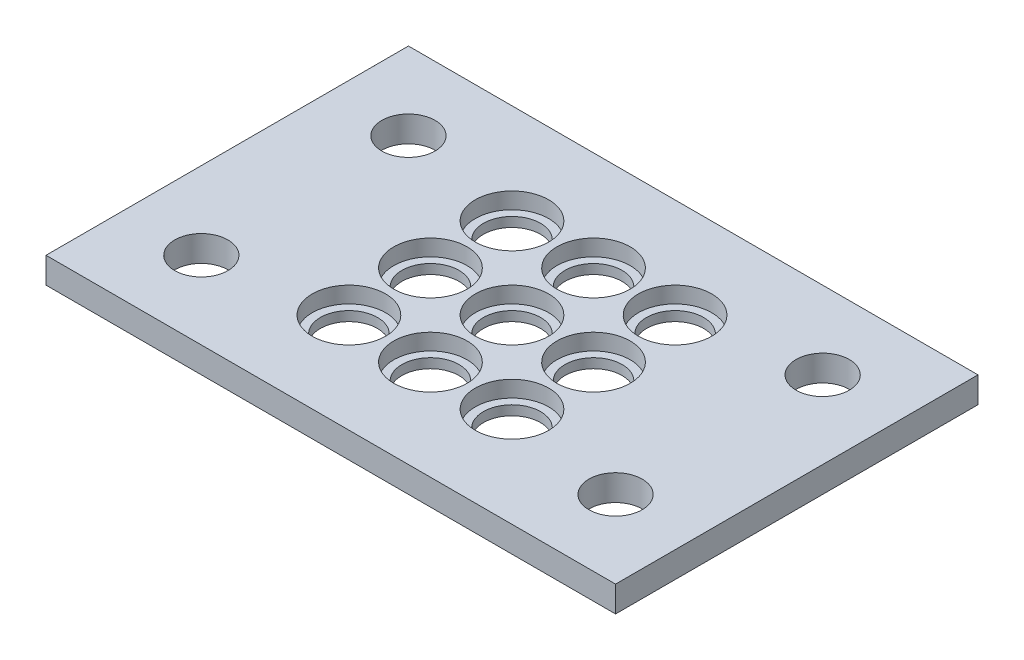
SolidWorks part; units mm, degrees
ref_plane "Front Plane" through (0, 0, 0) normal (0, 0, 1) x (1, 0, 0)
ref_plane "Top Plane" through (0, 0, 0) normal (0, 1, 0) x (1, 0, 0)
ref_plane "Right Plane" through (0, 0, 0) normal (1, 0, 0) x (0, 0, -1)
sketch "Sketch1" plane through (0, 0, 0) normal (0, 1, 0) x (1, 0, 0)
  line L0 (9.525, 34.925) -> (0, 34.925) construction
  line L1 (0, 0) -> (69.85, 0)
  line L2 (0, 0) -> (0, 44.45)
  line L3 (0, 44.45) -> (69.85, 44.45)
  line L4 (69.85, 0) -> (69.85, 44.45)
  line L5 (9.525, 34.925) -> (60.325, 34.925) construction
  line L6 (9.525, 34.925) -> (9.525, 9.525) construction
  line L7 (9.525, 9.525) -> (60.325, 9.525) construction
  line L8 (60.325, 34.925) -> (60.325, 9.525) construction
  line L9 (9.525, 34.925) -> (9.525, 44.45) construction
  circle A0 centre (9.525, 34.925) radius 3.2639
  circle A1 centre (60.325, 34.925) radius 3.2639
  circle A2 centre (9.525, 9.525) radius 3.2639
  circle A3 centre (60.325, 9.525) radius 3.2639
  circle A4 centre (44.925, 32.225) radius 3.5
  circle A5 centre (34.925, 32.225) radius 3.5
  circle A6 centre (24.925, 32.225) radius 3.5
  circle A7 centre (34.925, 22.225) radius 3.5
  circle A8 centre (24.925, 22.225) radius 3.5
  circle A9 centre (34.925, 12.225) radius 3.5
  circle A10 centre (24.925, 12.225) radius 3.5
  circle A11 centre (44.925, 22.225) radius 3.5
  circle A12 centre (44.925, 12.225) radius 3.5
  point P13 (34.925, 34.925)
  point P14 (34.925, 44.45)
  point P19 (0, 0)
  point P20 (0, 22.225)
  dimension "D5" = 6.5278
  dimension "D6" = 7
  dimension "D1" = 69.85
  dimension "D2" = 44.45
  dimension "D3" = 50.8
  dimension "D4" = 25.4
  dimension "D7" = 3
  dimension "D8" = 3
extrude "Boss-Extrude1" add sketch "Sketch1" along normal blind 3.175
sketch "Sketch2" plane through (0, 3.175, 0) normal (0, 1, 0) x (1, 0, 0)
  circle A0 centre (44.925, 12.225) radius 4.5
  circle A1 centre (44.925, 12.225) radius 3.5 construction
  circle A2 centre (34.925, 12.225) radius 4.5
  circle A3 centre (24.925, 12.225) radius 4.5
  circle A4 centre (34.925, 22.225) radius 4.5
  circle A5 centre (24.925, 22.225) radius 4.5
  circle A6 centre (34.925, 32.225) radius 4.5
  circle A7 centre (24.925, 32.225) radius 4.5
  circle A8 centre (44.925, 22.225) radius 4.5
  circle A9 centre (44.925, 32.225) radius 4.5
  dimension "D1" = 9
  dimension "D2" = 3
  dimension "D3" = 3
extrude "Cut-Extrude1" cut sketch "Sketch2" against normal blind 2
